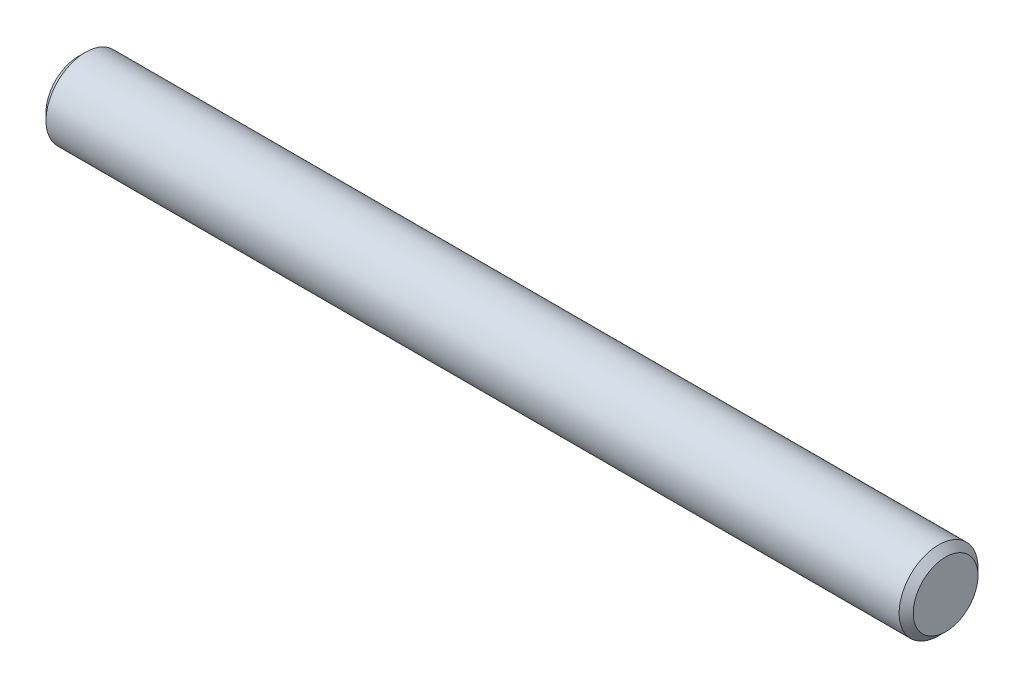
SolidWorks part; units mm, degrees
ref_plane "Plane1" through (0, 0, 0) normal (0, 0, 1) x (1, 0, 0)
ref_plane "Plane2" through (0, 0, 0) normal (0, 1, 0) x (1, 0, 0)
ref_plane "Plane3" through (0, 0, 0) normal (1, 0, 0) x (0, 0, -1)
sketch "BodySke" plane through (0, 0, 0) normal (0, 0, 1) x (1, 0, 0)
  line L0 (50.89, 15.875) -> (50.89, -6.35) construction
  line L1 (0.8, 15.875) -> (0.8, -3.175) construction
  line L2 (55, 6.35) -> (55, 3.175) construction
  line L10 (0, 2.5) -> (55, 2.5)
  line L12 (55, 2.5) -> (55, 0)
  line L13 (55, 0) -> (0, 0)
  line L14 (-3.175, 0) -> (107.95, 0) construction
  line L18 (0, 2.5) -> (0, 0)
  dimension "Diameter" = 5
  dimension "Minor_dia" = 4.11
  dimension "Length" = 55
  dimension "Advance" = 0.8
  dimension "Thread_max" = 55
revolve "BaseBody" add sketch "BodySke" angle 360 about L14
cosmetic thread "ThreadCosmetic" [suppressed] parameters "Thread_minor"=4.11
chamfer "Chamfer1" distance 0.445 angle 45 2 edges at (0, 0, 2.5) (55, 0, 2.5)
sketch "ThdSchSke" plane through (0, 0, 0) normal (0, 0, 1) x (1, 0, 0)
  line L0 (0.3116, -2.055) -> (0, -2.5)
  line L1 (0.3116, -2.055) -> (0.6232, -2.5)
  line L2 (0.6232, -2.5) -> (0.6232, -3.125)
  line L3 (-3.175, 0) -> (5.1513, 0) construction
  line L4 (0, 2.5) -> (0, -2.5) construction
  line L5 (0.6232, -3.125) -> (0, -3.125)
  line L6 (0, -3.125) -> (0, -2.5)
  dimension "Thread_minor" = 4.11
  dimension "Diameter" = 5
  dimension "SideAngle" = 55
  dimension "VeeAngle" = 70
  dimension "Overcut" = 6.25
revolve "ThreadSchematic" [suppressed] cut sketch "ThdSchSke" angle 360 about L3
pattern_linear "ThdSchPat" [suppressed]
equation "\"Thread_minor@ThreadCosmetic\" = \"Minor_dia@BodySke\""
equation "\"Chamfer@Chamfer1\" =  ( \"Diameter@BodySke\" - \"Minor_dia@BodySke\" ) / 2"
equation "\"Thread_minor@ThdSchSke\" = \"Minor_dia@BodySke\""
equation "\"Diameter@ThdSchSke\" = \"Diameter@BodySke\""
equation "\"Overcut@ThdSchSke\" = \"Diameter@BodySke\" * 1.25"
equation "\"Num_threads@ThdSchPat\" = int( (\"Thread_max@BodySke\" - \"Advance@BodySke\" ) / \"Advance@BodySke\" + 0.999 ) + 1"
equation "\"Advance@ThdSchPat\" = \"Thread_max@BodySke\" /  ( \"Num_threads@ThdSchPat\" - 1 ) 'relax it"
equation "\"Num_threads@ThdSchPat\" = \"Num_threads@ThdSchPat\" - sgn( \"Num_threads@ThdSchPat\" - 1 ) '---chamfered tips only---"
